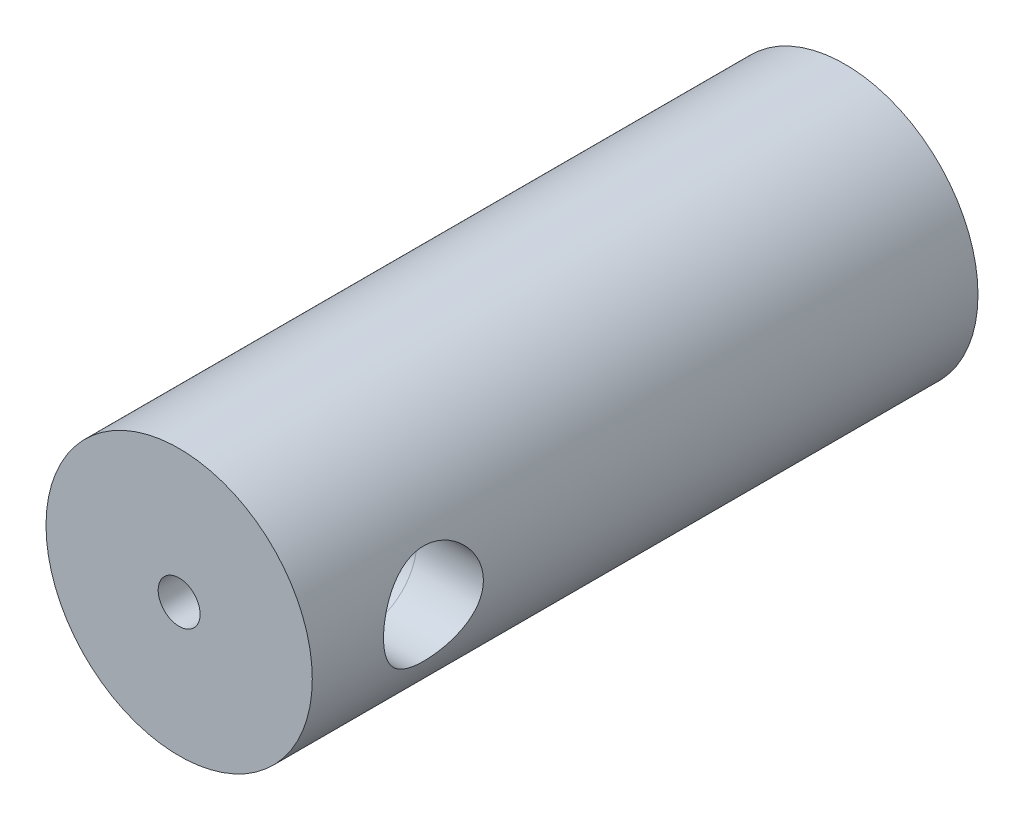
SolidWorks part; units mm, degrees
ref_plane "Front Plane" through (0, 0, 0) normal (0, 0, 1) x (1, 0, 0)
ref_plane "Top Plane" through (0, 0, 0) normal (0, 1, 0) x (1, 0, 0)
ref_plane "Right Plane" through (0, 0, 0) normal (1, 0, 0) x (0, 0, -1)
sketch "Sketch1" plane through (0, 0, 0) normal (0, 0, 1) x (1, 0, 0)
  circle A0 centre (0, 0) radius 20
  dimension "D1" = 40
extrude "Boss-Extrude1" add sketch "Sketch1" along normal blind 100
sketch "Sketch2" plane through (0, 0, 0) normal (0, 0, -1) x (-1, 0, 0)
  circle A0 centre (0, 0) radius 7.5
  dimension "D1" = 15
sketch "Sketch3" plane through (0, 0, 100) normal (0, 0, 1) x (1, 0, 0)
  circle A0 centre (0, 0) radius 3.15
  dimension "D1" = 6.3
extrude "Cut-Extrude2" cut sketch "Sketch3" against normal blind 5
sketch "Sketch4" plane through (0, 0, 0) normal (0, 1, 0) x (1, 0, 0)
  line L0 (0, 0) -> (0, -71.7939)
  line L1 (10, -81.7939) -> (20, -81.7939)
  line L3 (20, -100) -> (20, 0) construction
  arc A0 (0, -71.7939) -> (10, -81.7939) centre (10, -71.7939) ccw
  dimension "D1" = 10
sweep "Cut-Sweep1" cut profiles "Sketch2" path "Sketch4"
sketch "Sketch5" plane through (0, 0, 0) normal (0, 0, -1) x (-1, 0, 0)
  circle A0 centre (0, 0) radius 9.75
  dimension "D1" = 19.5
sketch "Sketch6" plane through (0, 0, 0) normal (0, 0, 1) x (1, 0, 0)
  line L0 (0, 0) -> (0, 15.3412) construction
  line L1 (0, 9.75) -> (8.0888, 9.75) construction
  line L2 (8.0888, 9.75) -> (-7.2183, 9.75) construction
  line L4 (2.5, 13.75) -> (-2.5, 13.75)
  line L5 (2.5, 13.75) -> (2.5, 6.4577)
  line L6 (2.5, 6.4577) -> (-2.5, 6.4577)
  line L7 (-2.5, 13.75) -> (-2.5, 6.4577)
  circle A0 centre (0, 0) radius 9.75
  dimension "D1" = 19.5
  dimension "D2" = 2.5
  dimension "D3" = 5
  dimension "D4" = 4
extrude "Cut-Extrude3" cut sketch "Sketch6" along normal blind 10 contours L7 A0 L5 L6
